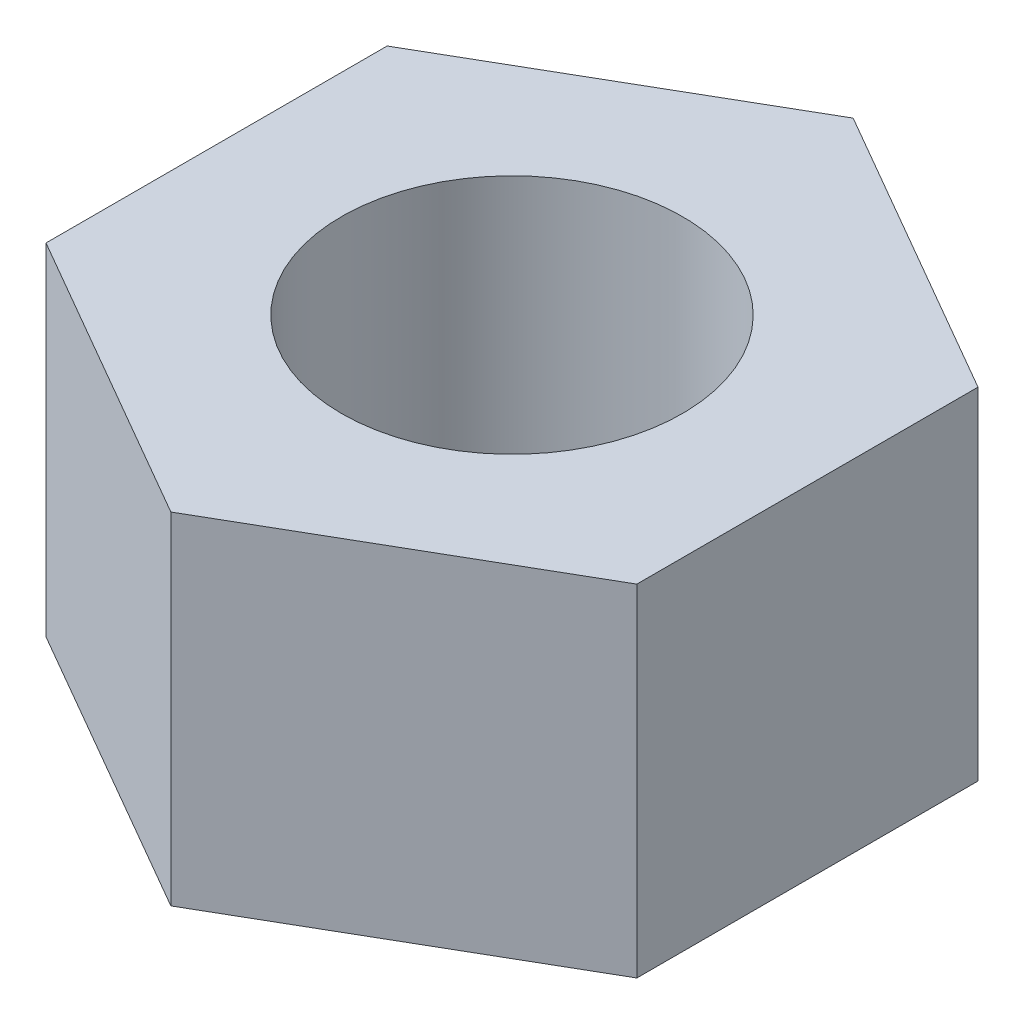
SolidWorks part; units mm, degrees
ref_plane "Front Plane" through (0, 0, 0) normal (0, 0, 1) x (1, 0, 0)
ref_plane "Top Plane" through (0, 0, 0) normal (0, 1, 0) x (1, 0, 0)
ref_plane "Right Plane" through (0, 0, 0) normal (1, 0, 0) x (0, 0, -1)
sketch "Sketch1" plane through (0, 0, 0) normal (0, 1, 0) x (1, 0, 0)
  line L1 (0, 9) -> (-7.7942, 4.5)
  line L2 (-7.7942, 4.5) -> (-7.7942, -4.5)
  line L3 (-7.7942, -4.5) -> (0, -9)
  line L4 (0, -9) -> (7.7942, -4.5)
  line L5 (7.7942, -4.5) -> (7.7942, 4.5)
  line L6 (7.7942, 4.5) -> (0, 9)
  circle A0 centre (0, 0) radius 7.7942 construction
  dimension "D1" = 9
extrude "Boss-Extrude1" add sketch "Sketch1" along normal blind 9
sketch "Sketch2" plane through (0, 9, 0) normal (0, 1, 0) x (1, 0, 0)
  circle A0 centre (0, 0) radius 4.5
  dimension "D1" = 9
extrude "Cut-Extrude1" cut sketch "Sketch2" against normal blind 9
